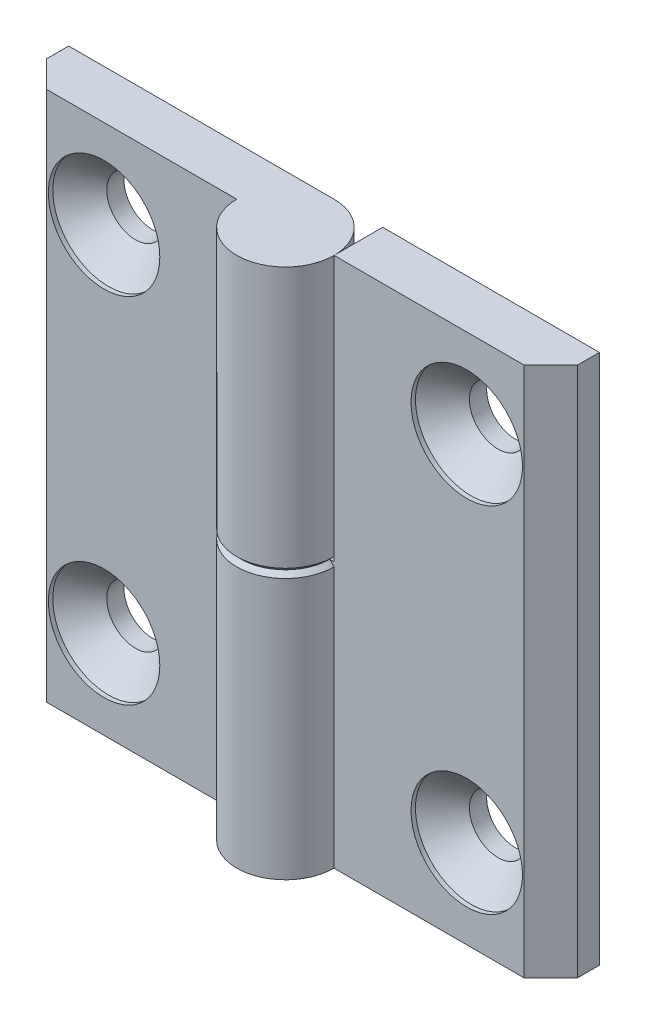
SolidWorks part; units mm, degrees
material "Алюминиевый сплав"
ref_plane "Спереди" through (0, 0, 0) normal (0, 0, 1) x (1, 0, 0)
ref_plane "Сверху" through (0, 0, 0) normal (0, 1, 0) x (1, 0, 0)
ref_plane "Справа" through (0, 0, 0) normal (1, 0, 0) x (0, 0, -1)
sketch "Эскиз1" plane through (0, 0, 0) normal (0, 1, 0) x (1, 0, 0)
  line L0 (0, 5.5) -> (-30, 5.5)
  line L1 (-30, 5.5) -> (-30, 3)
  line L2 (-30, 3) -> (-27, 0)
  line L3 (-27, 0) -> (-5.5, 0)
  line L4 (0, 0) -> (0, 10.5526) construction
  arc A0 (-5.5, 0) -> (0, 5.5) centre (0, 0) ccw
  dimension "D1" = 60
  dimension "D2" = 5.5
  dimension "D3" = 2.5
  dimension "D4" = 45
extrude "Бобышка-Вытянуть1" add sketch "Эскиз1" along normal mid plane 60
sketch "Эскиз3" plane through (0, 0, 0) normal (0, 0, 1) x (1, 0, 0)
  line L5 (-5.5, 30) -> (-5.5, -30) construction
  line L6 (5.5, -30) -> (-5.5, -30)
  line L7 (5.5, -30) -> (5.5, 0)
  line L8 (5.5, 0) -> (-5.5, 0)
  line L9 (-5.5, -30) -> (-5.5, 0)
extrude "Вырез-Вытянуть1" cut sketch "Эскиз3" against normal through all and the other way through all
hole_wizard "Зенковка для винта с полупотайной головкой M61" positions "Эскиз4" profile "Эскиз6" countersink size "M6" standard "ISO" end condition through all
sketch "Эскиз4" plane through (0, 0, 0) normal (0, 0, 1) x (1, 0, 0)
  line L0 (-20.5, 20) -> (-20.5, -20)
  line L2 (0, 0) -> (0, 18.9001) construction
  point P0 (-20.5, 20)
  point P2 (-20.5, -20)
  point P9 (-20.5, 0)
  dimension "D1" = 40
  dimension "D2" = 41
sketch "Эскиз6" plane through (-20.5, 20, 0) normal (1, 0, 0) x (0, -1, 0)
  line L0 (0, 0) -> (0, 5.5)
  line L1 (0, 5.5) -> (3.25, 5.5)
  line L2 (3.25, 5.5) -> (3.25, 3.55)
  line L3 (3.25, 3.55) -> (6.3, 0.5)
  line L4 (6.3, 0.5) -> (6.3, 0)
  line L6 (6.3, 0) -> (0, 0)
  line L7 (-3.25, 3.55) -> (-6.3, 0.5) construction
  line L11 (0, -6.35) -> (0, 107.95) construction
  dimension "Диаметр сквозного отверстия" = 6.5
  dimension "Глубина сквозного отверстия" = 5.5
  dimension "Диаметр зенковки" = 12.6
  dimension "Угол зенковки" = 90
  dimension "Утопленность" = 0.5
chamfer "Фаска1" distance 0.5 angle 45 2 edges at (-2.75, 0, -5.5) (3.8891, 0, 3.8891)
sketch "Угол раскрытия" plane through (0, 0, 0) normal (0, 1, 0) x (1, 0, 0)
  line L0 (0, 0) -> (0, -10)
  line L7 (0, 5.5) -> (-30, 5.5) construction
  dimension "D1" = 10
  dimension "D2" = 90
pattern_circular "Круговой массив1" count 2 over 360 about axis through (0, 0, 0) along (0, 0, 1) of bodies 106
